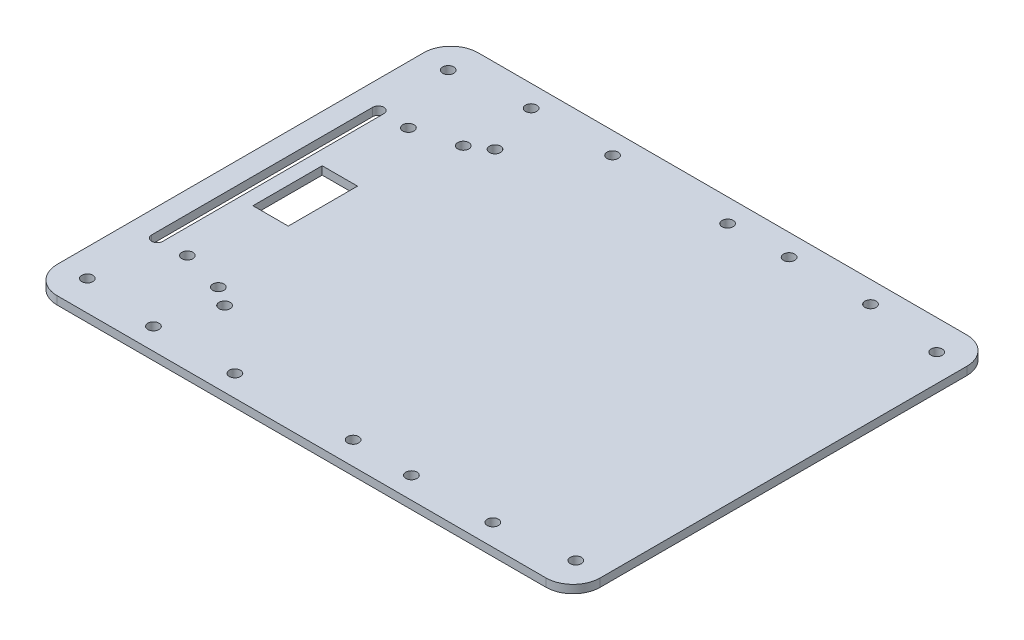
SolidWorks part; units mm, degrees
material "1060 Alloy"
ref_plane "Front Plane" through (0, 0, 0) normal (0, 0, 1) x (1, 0, 0)
ref_plane "Top Plane" through (0, 0, 0) normal (0, 1, 0) x (1, 0, 0)
ref_plane "Right Plane" through (0, 0, 0) normal (1, 0, 0) x (0, 0, -1)
sketch "Sketch1" plane through (0, 0, 0) normal (0, 1, 0) x (1, 0, 0)
  line L1 (0, 0) -> (200, 0)
  line L2 (0, 0) -> (0, 155)
  line L3 (0, 155) -> (200, 155)
  line L4 (200, 0) -> (200, 155)
  dimension "D1" = 200
  dimension "D2" = 155
extrude "Boss-Extrude1" add sketch "Sketch1" along normal blind 3
sketch "Sketch2" plane through (0, 3, 0) normal (0, 1, 0) x (1, 0, 0)
  line L0 (0, 10) -> (200, 10) construction
  line L1 (0, 155) -> (0, 0) construction
  line L2 (200, 0) -> (200, 155) construction
  line L3 (0, 0) -> (200, 0) construction
  line L4 (0, 7.95) -> (200, 7.95) construction
  line L5 (0, 77.5) -> (200, 77.5) construction
  line L6 (0, 147.05) -> (200, 147.05) construction
  circle A0 centre (37.5, 7.95) radius 2.05
  circle A1 centre (67.5, 7.95) radius 2.05
  circle A2 centre (132.5, 7.95) radius 2.05
  circle A3 centre (162.5, 7.95) radius 2.05
  circle A4 centre (162.5, 147.05) radius 2.05
  circle A5 centre (132.5, 147.05) radius 2.05
  circle A6 centre (67.5, 147.05) radius 2.05
  circle A7 centre (37.5, 147.05) radius 2.05
  dimension "D2" = 4.1
  dimension "D1" = 10
  dimension "D3" = 7.95
  dimension "D4" = 37.5
  dimension "D5" = 30
  dimension "D6" = 30
  dimension "D7" = 37.5
extrude "Cut-Extrude1" cut sketch "Sketch2" against normal through all contours A0 | A1 | A2 | A3 | A7 | A6 | A5 | A4
fillet "Fillet1" radius 10 4 edges at (200, 1.5, -155) (200, 1.5, 0) (0, 1.5, 0) (0, 1.5, -155)
ref_plane "Plane4" through (0, 0, -77.5) normal (0, 0, -1) x (-1, 0, 0)
sketch "Sketch5" plane through (0, 0, -77.5) normal (0, 0, -1) x (-1, 0, 0)
  line L0 (2.8863, -2.1819) -> (9.9208, -27)
  line L1 (5.7726, -1.3638) -> (13.0389, -27)
  line L2 (0, 3) -> (0, 5.4755) construction
  line L3 (13.0389, -27) -> (9.9208, -27)
  line L4 (0, 3) -> (-10, 3) construction
  line L5 (0, 3) -> (0, 0)
  arc A0 (5.7726, -1.3638) -> (0, 3) centre (0, -3) ccw
  arc A1 (2.8863, -2.1819) -> (0, 0) centre (0, -3) ccw
  dimension "D4" = 6
  dimension "D1" = 30
  dimension "D2" = 3
  dimension "D3" = 3.1182
sketch "Sketch6" plane through (0, 3, 0) normal (0, 1, 0) x (1, 0, 0)
  line L0 (8, 155) -> (8, 0) construction
  line L1 (190, 155) -> (10, 155) construction
  line L2 (10, 0) -> (190, 0) construction
  line L3 (0, 145) -> (0, 10) construction
  line L4 (0, 146) -> (200, 146) construction
  line L5 (10.05, 118.2) -> (10.05, 36.8) construction
  line L6 (12.1, 118.2) -> (12.1, 36.8)
  line L7 (8, 118.2) -> (8, 36.8)
  line L8 (0, 77.5) -> (200, 77.5) construction
  line L9 (30.35, 64.75) -> (17.35, 64.75)
  line L10 (30.35, 64.75) -> (30.35, 90.25)
  line L11 (30.35, 90.25) -> (17.35, 90.25)
  line L12 (17.35, 64.75) -> (17.35, 90.25)
  line L13 (30.35, 64.75) -> (17.35, 90.25) construction
  line L14 (30.35, 90.25) -> (17.35, 64.75) construction
  line L15 (200, 10) -> (200, 145) construction
  line L16 (0, 9) -> (200, 9) construction
  line L17 (189.95, 155) -> (189.95, 0) construction
  line L18 (110.45, 155) -> (110.45, 0) construction
  circle A0 centre (10.05, 143.95) radius 2.05
  arc A1 (12.1, 118.2) -> (8, 118.2) centre (10.05, 118.2) ccw
  arc A2 (8, 36.8) -> (12.1, 36.8) centre (10.05, 36.8) ccw
  circle A3 centre (21.15, 118.2) radius 2.05
  circle A4 centre (36.95, 122.6) radius 2.05
  circle A5 centre (43.95, 127.3) radius 2.05
  circle A6 centre (43.95, 27.7) radius 2.05
  circle A7 centre (36.95, 32.4) radius 2.05
  circle A8 centre (10.05, 11.05) radius 2.05
  circle A9 centre (21.15, 36.8) radius 2.05
  circle A10 centre (189.95, 143.95) radius 2.05
  circle A11 centre (110.45, 146.45) radius 2.05
  circle A12 centre (189.95, 11.05) radius 2.05
  circle A13 centre (110.45, 8.55) radius 2.05
  point P15 (10.05, 77.5)
  point P20 (10.05, 120.25)
  point P21 (10.05, 34.75)
  point P25 (23.85, 77.5)
  dimension "D3" = 4.1
  dimension "D1" = 8
  dimension "D2" = 9
  dimension "D4" = 34.75
  dimension "D5" = 34.75
  dimension "D6" = 8
  dimension "D7" = 9.05
  dimension "D8" = 5.25
  dimension "D9" = 64.75
  dimension "D10" = 64.75
  dimension "D11" = 13
  dimension "D12" = 163.05
  dimension "D13" = 32.4
  dimension "D14" = 156.05
  dimension "D15" = 27.7
  dimension "D16" = 10.05
  dimension "D17" = 11.05
  dimension "D18" = 89.55
  dimension "D19" = 8.55
extrude "Cut-Extrude2" cut sketch "Sketch6" against normal through all
